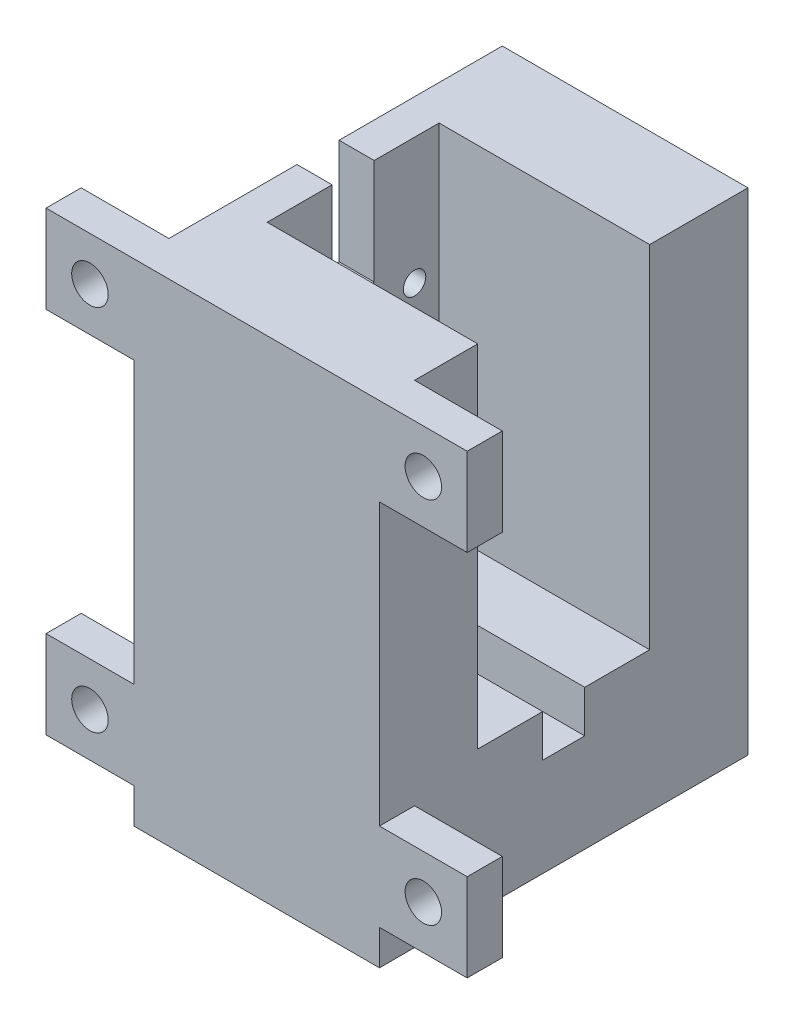
SolidWorks part; units mm, degrees
ref_plane "Front Plane" through (0, 0, 0) normal (0, 0, 1) x (1, 0, 0)
ref_plane "Top Plane" through (0, 0, 0) normal (0, 1, 0) x (1, 0, 0)
ref_plane "Right Plane" through (0, 0, 0) normal (1, 0, 0) x (0, 0, -1)
sketch "Sketch1" plane through (0, 0, 0) normal (0, 0, 1) x (1, 0, 0)
  line L1 (0, 0) -> (40, 0)
  line L2 (0, 0) -> (0, 65)
  line L3 (0, 65) -> (40, 65)
  line L4 (40, 0) -> (40, 65)
  dimension "D1" = 65
  dimension "D2" = 40
extrude "Boss-Extrude1" add sketch "Sketch1" along normal blind 42.5 and the other way blind 15
sketch "Sketch3" plane through (40, 0, 0) normal (1, 0, 0) x (0, 0, -1)
  line L0 (15, 15) -> (0, 15)
  line L1 (15, 0) -> (15, 65) construction
  line L2 (0, 65) -> (0, 15)
  line L3 (15, 65) -> (-42.5, 65) construction
  line L4 (15, 0) -> (-42.5, 0) construction
  line L5 (-22.5, 65) -> (-22.5, 15)
  line L6 (-22.5, 15) -> (0, 15)
  line L7 (-22.5, 65) -> (0, 65)
  line M4 (15, 65) -> (-42.5, 65)
  dimension "D1" = 15
  dimension "D2" = 15
  dimension "D3" = 22.5
extrude "Cut-Extrude2" cut sketch "Sketch3" against normal blind 30 contours L5 L6 L2 M4
sketch "Sketch4" plane through (10, 0, 0) normal (1, 0, 0) x (0, 0, -1)
  line L0 (-11.25, 15) -> (-11.25, 26.5) construction
  line L1 (-22.5, 15) -> (0, 15) construction
  circle A0 centre (-11.25, 26.5) radius 4.5
  dimension "D2" = 9
  dimension "D1" = 11.5
extrude "Cut-Extrude3" cut sketch "Sketch4" against normal blind 10
sketch "Sketch5" plane through (0, 0, 0) normal (0, -1, 0) x (1, 0, 0)
  line L0 (40, 17.5) -> (70, 17.5)
  line L1 (70, 17.5) -> (70, 42.5)
  line L2 (70, 42.5) -> (40, 42.5)
  line L3 (40, 42.5) -> (40, 17.5)
  line L6 (63.817, 25.1893) -> (35.817, 25.1893) construction
  line L8 (40, -15) -> (40, 42.5) construction
  circle A0 centre (63.817, 25.1893) radius 3 construction
  circle A1 centre (35.817, 25.1893) radius 3 construction
  dimension "D1" = 28
  dimension "D2" = 30
  dimension "D3" = 25
sketch "Sketch6" plane through (0, 0, 42.5) normal (0, 0, 1) x (1, 0, 0)
  line L0 (40, 65) -> (40, 0)
  line L1 (40, 0) -> (0, 0)
  line L2 (0, 0) -> (0, 65)
  line L3 (0, 65) -> (40, 65)
extrude "Cut-Extrude4" cut sketch "Sketch6" against normal blind 5
sketch "Sketch7" plane through (0, 0, 0) normal (0, -1, 0) x (1, 0, 0)
  line L0 (40, 42.5) -> (40, 17.5) construction
  line L1 (0, 37.5) -> (40, 37.5) construction
  line L2 (28, 25.5) -> (28, -3) construction
  line L3 (40, -15) -> (40, 11.25) construction
  line L4 (40, -15) -> (40, 37.5) construction
  line L5 (40, 11.25) -> (13.6736, 11.25) construction
  circle A0 centre (28, 25.5) radius 3
  circle A1 centre (28, -3) radius 3
  point P13 (28, 11.25)
  dimension "D1" = 6
  dimension "D3" = 12
  dimension "D4" = 6
  dimension "D2" = 12
extrude "Cut-Extrude5" cut sketch "Sketch7" against normal blind 10
sketch "Sketch8" plane through (0, 0, 0) normal (-1, 0, 0) x (0, 0, 1)
  line L4 (37.5, 0) -> (37.5, 65)
  line L5 (37.5, 65) -> (-15, 65)
  line L6 (-15, 65) -> (-15, 0)
  line L7 (-15, 0) -> (37.5, 0)
  line L8 (37.5, 0) -> (37.5, 65)
  line L9 (37.5, 65) -> (-15, 65)
  line L10 (-15, 65) -> (-15, 0)
  line L11 (-15, 0) -> (37.5, 0)
  dimension "D1" = 0
extrude "Cut-Extrude6" cut sketch "Sketch8" against normal blind 5
ref_plane "Plane1" through (0, 0, 37.5) normal (0, 0, 1) x (1, 0, 0)
sketch "Sketch9" plane through (0, 0, 37.5) normal (0, 0, 1) x (1, 0, 0)
  line L0 (5, 65) -> (-7.5, 65)
  line L1 (-7.5, 65) -> (-7.5, 52.5)
  line L2 (-7.5, 52.5) -> (5, 52.5)
  line L3 (5, 65) -> (5, 0) construction
  line L4 (22.5, 0) -> (22.5, 65) construction
  line L5 (5, 0) -> (40, 0) construction
  line L6 (40, 65) -> (5, 65) construction
  line L7 (5, 32.5) -> (40, 32.5) construction
  line L8 (40, 0) -> (40, 65) construction
  line L9 (5, 52.5) -> (5, 65)
  line L10 (40, 52.5) -> (40, 65)
  line L11 (40, 65) -> (52.5, 65)
  line L12 (52.5, 65) -> (52.5, 52.5)
  line L13 (52.5, 52.5) -> (40, 52.5)
  line L14 (40, 0) -> (52.5, 0)
  line L15 (52.5, 0) -> (52.5, 12.5)
  line L16 (52.5, 12.5) -> (40, 12.5)
  line L17 (40, 12.5) -> (40, 0)
  line L18 (5, 12.5) -> (5, 0)
  line L19 (5, 0) -> (-7.5, 0)
  line L20 (-7.5, 0) -> (-7.5, 12.5)
  line L21 (-7.5, 12.5) -> (5, 12.5)
  circle A0 centre (-1.25, 58.75) radius 2.6
  circle A1 centre (46.25, 58.75) radius 2.6
  circle A2 centre (46.25, 6.25) radius 2.6
  circle A3 centre (-1.25, 6.25) radius 2.6
  dimension "D1" = 5.2
extrude "Boss-Extrude2" add sketch "Sketch9" against normal blind 5
sketch "Sketch10" plane through (0, 0, 0) normal (0, -1, 0) x (1, 0, 0)
  line L0 (40, 32.5) -> (40, 37.5)
  line L2 (5, -15) -> (5, 32.5) construction
  line L3 (5, -15) -> (5, 37.5)
  line L8 (52.5, 37.5) -> (-7.5, 37.5)
  line L9 (-7.5, 37.5) -> (-7.5, 32.5)
  line L10 (-7.5, 32.5) -> (5, 32.5)
  line L11 (5, 32.5) -> (5, -15)
  line L12 (5, -15) -> (40, -15)
  line L13 (40, -15) -> (40, 32.5)
  line L14 (40, 32.5) -> (52.5, 32.5)
  line L15 (52.5, 32.5) -> (52.5, 37.5)
  line L16 (40, 37.5) -> (5, 37.5)
  line L20 (5, -15) -> (40, -15)
  line L21 (40, -15) -> (40, 32.5)
  circle A0 centre (28, 25.5) radius 3 construction
  circle A1 centre (28, -3) radius 3 construction
  circle A2 centre (28, 25.5) radius 3
  circle A3 centre (28, -3) radius 3
  dimension "D1" = 0
extrude "Boss-Extrude3" add sketch "Sketch10" along normal blind 5
sketch "Sketch11" plane through (10, 0, 0) normal (1, 0, 0) x (0, 0, -1)
  circle A0 centre (-2.5, 47) radius 1.6
  circle A1 centre (-20, 47) radius 1.6
  dimension "D1" = 3.2
  dimension "D2" = 3.2
extrude "Cut-Extrude7" cut sketch "Sketch11" against normal through all
ref_plane "Plane2" through (0, 0, 11.25) normal (0, 0, -1) x (-1, 0, 0)
sketch "Sketch12" plane through (0, 0, 11.25) normal (0, 0, -1) x (-1, 0, 0)
  line L0 (-40, 65) -> (-40, 15)
  line L1 (-40, 15) -> (-10, 15)
  line L2 (-10, 15) -> (-10, 65)
  line L3 (-10, 65) -> (-40, 65)
extrude "Cut-Extrude8" cut sketch "Sketch12" against normal blind 12.25 and the other way blind 12.25
sketch "Sketch13" plane through (40, 0, 0) normal (1, 0, 0) x (0, 0, -1)
  line L0 (-11.25, 15) -> (-11.25, 1.5513) construction
  line L1 (-23.5, 15) -> (1, 15) construction
  line L2 (-11.25, -55) -> (-11.25, 55) construction
  line L3 (-11.25, 15) -> (-8.25, 15)
  line L4 (-23.5, 15) -> (1, 15) construction
  line L5 (-8.25, 15) -> (-8.25, 9)
  line L6 (-8.25, 9) -> (-14.25, 9)
  line L7 (-14.25, 9) -> (-14.25, 15)
  line L8 (-14.25, 15) -> (-11.25, 15)
extrude "Cut-Extrude9" cut sketch "Sketch13" against normal up to surface (30 mm away) up to face at (10, 47, 0.9)
sketch "Sketch14" plane through (0, 65, 0) normal (0, 1, 0) x (1, 0, 0)
  line L0 (10, -11.25) -> (5, -11.25) construction
  line L1 (10, 1) -> (10, -23.5) construction
  line L2 (55, -11.25) -> (-55, -11.25) construction
  line L3 (5, -32.5) -> (5, 15) construction
  line L4 (5, -11.25) -> (5, -8.25)
  line L5 (5, -8.25) -> (10, -8.25)
  line L6 (10, -8.25) -> (10, 1) construction
  line L7 (10, -8.25) -> (10, -14.25)
  line L8 (10, -8.25) -> (10, -14.25) construction
  line L9 (10, -14.25) -> (5, -14.25)
  line L10 (5, -14.25) -> (5, -11.25)
extrude "Cut-Extrude10" cut sketch "Sketch14" against normal blind 15
